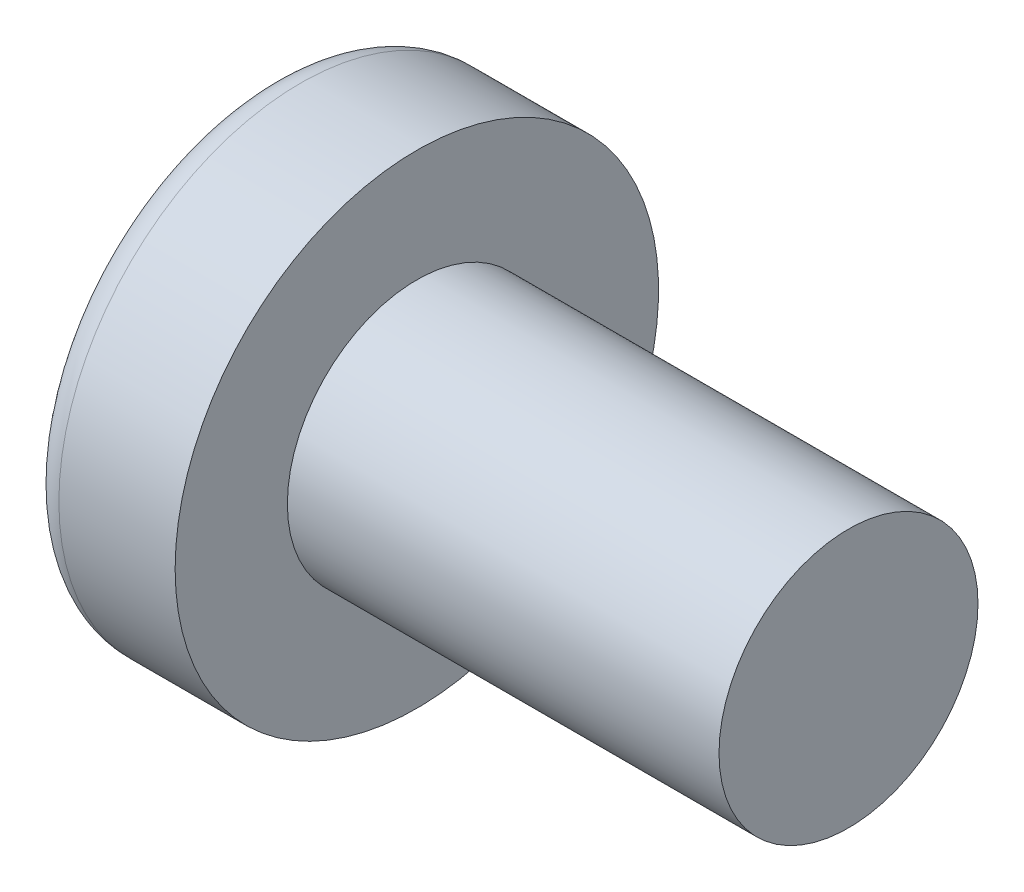
SolidWorks part; units mm, degrees
ref_plane "Plane1" through (0, 0, 0) normal (0, 0, 1) x (1, 0, 0)
ref_plane "Plane2" through (0, 0, 0) normal (0, 1, 0) x (1, 0, 0)
ref_plane "Plane3" through (0, 0, 0) normal (1, 0, 0) x (0, 0, -1)
sketch "BodySke" plane through (0, 0, 0) normal (0, 0, 1) x (1, 0, 0)
  line L0 (2.4, 1.5) -> (2.4, 2.8)
  line L1 (2.9, 6.35) -> (2.9, -3.175) construction
  line L2 (-25.4, 0) -> (127, 0) construction
  line L3 (7.4, 0) -> (0, 0)
  line L4 (2.4, 1.5) -> (7.4, 1.5)
  line L5 (7.4, 1.5) -> (7.4, 0)
  line L6 (1.0534, 2.8) -> (2.4, 2.8)
  line L7 (2.4, -1.5) -> (7.4, -1.5) construction
  line L8 (2.4, 6.35) -> (2.4, -3.175) construction
  arc A0 (0.7472, 2.6293) -> (0, 0) centre (5, 0) ccw
  arc A2 (0.7472, 2.6293) -> (1.0534, 2.8) centre (1.0534, 2.44) cw
  dimension "Head_fillet_rad" = 0.36
  dimension "Head_crown_rad" = 5
  dimension "Head_ht" = 2.4
  dimension "Diameter" = 3
  dimension "Length" = 5
  dimension "Head_dia" = 5.6
  dimension "Advance" = 0.5
  dimension "Thread_nom" = 5
revolve "Base-Revolve" add sketch "BodySke" angle 360 about L2
cosmetic thread "ThreadCosmetic" [suppressed] parameters "Thread_length"=4.5, "Thread_minor"=2.439
sketch "Sketch3" plane through (0, 0, 0) normal (1, 0, 0) x (0, 0, -1)
  line L0 (0.37, -1.45) -> (-0.37, -1.45)
  line L1 (0.37, -1.45) -> (0.37, 1.45)
  line L2 (-0.37, 1.45) -> (0.37, 1.45)
  line L3 (-0.37, 1.45) -> (-0.37, -1.45)
  dimension "D1" = 1.45
  dimension "Cross_dia" = 2.9
  dimension "D2" = 0.37
  dimension "Cross_width" = 0.74
ref_plane "Plane4" through (1.76, 0, 0) normal (1, 0, 0) x (0, 0, -1)
sketch "Sketch4" plane through (1.76, 0, 0) normal (1, 0, 0) x (0, 0, -1)
  line L0 (0.185, -0.185) -> (-0.185, -0.185)
  line L1 (0.185, -0.185) -> (0.185, 0.185)
  line L2 (-0.185, 0.185) -> (0.185, 0.185)
  line L3 (-0.185, 0.185) -> (-0.185, -0.185)
  dimension "D1" = 0.37
  dimension "D2" = 0.37
  dimension "D3" = 0.185
  dimension "D4" = 0.185
loft "Cut-Loft1" cut profiles "Sketch3", "Sketch4"
pattern_circular "CirPattern1" count 2 every 90 about axis through (0, 0, 0) along (1, 0, 0) of "Cut-Loft1"
sketch "ThdSchSke" plane through (0, 0, 0) normal (0, 0, 1) x (1, 0, 0)
  line L0 (2.9, -1.2195) -> (2.7036, -1.5)
  line L1 (2.9, -1.2195) -> (3.0964, -1.5)
  line L2 (3.0964, -1.5) -> (3.0964, -1.875)
  line L3 (-3.175, 0) -> (5.1513, 0) construction
  line L5 (3.0964, -1.875) -> (2.7036, -1.875)
  line L6 (2.7036, -1.875) -> (2.7036, -1.5)
  dimension "Thread_minor" = 2.439
  dimension "Diameter" = 3
  dimension "Start" = 2.9
  dimension "SideAngle" = 55
  dimension "VeeAngle" = 70
  dimension "Overcut" = 3.75
revolve "ThreadSchematic" [suppressed] cut sketch "ThdSchSke" angle 360 about L3
pattern_linear "ThdSchPat" [suppressed]
equation "\"D1@Sketch3\" = \"Cross_dia@Sketch3\" / 2"
equation "\"D2@Sketch3\" = \"Cross_width@Sketch3\" / 2"
equation "\"D1@Sketch4\" = \"Cross_width@Sketch3\" *.5"
equation "\"D2@Sketch4\" = \"D1@Sketch4\""
equation "\"D3@Sketch4\" = \"D1@Sketch4\" / 2"
equation "\"D4@Sketch4\" = \"D2@Sketch4\" / 2"
equation "\"Thread_length@ThreadCosmetic\" = ((sgn( (\"Length@BodySke\" - \"Advance@BodySke\" ) - \"Thread_nom@BodySke\" )-1)*( (\"Length@BodySke\" - \"Advance@BodySke\" ) - \"Thread_nom@BodySke\" ))/-2+ \"Thread_nom@BodySke\""
equation "\"Thread_minor@ThdSchSke\" = \"Thread_minor@ThreadCosmetic\""
equation "\"Diameter@ThdSchSke\" = \"Diameter@BodySke\""
equation "\"Overcut@ThdSchSke\" = \"Diameter@BodySke\" * 1.25"
equation "\"Start@ThdSchSke\" = \"Head_ht@BodySke\" + \"Length@BodySke\" - \"Thread_length@ThreadCosmetic\"  '---Non-countersunk---"
equation "\"Num_threads@ThdSchPat\" = int( \"Thread_length@ThreadCosmetic\" / \"Advance@BodySke\" + 0.999 )  + 1"
equation "\"Advance@ThdSchPat\" = \"Thread_length@ThreadCosmetic\" /  (\"Num_threads@ThdSchPat\" - 1) 'relax it"
